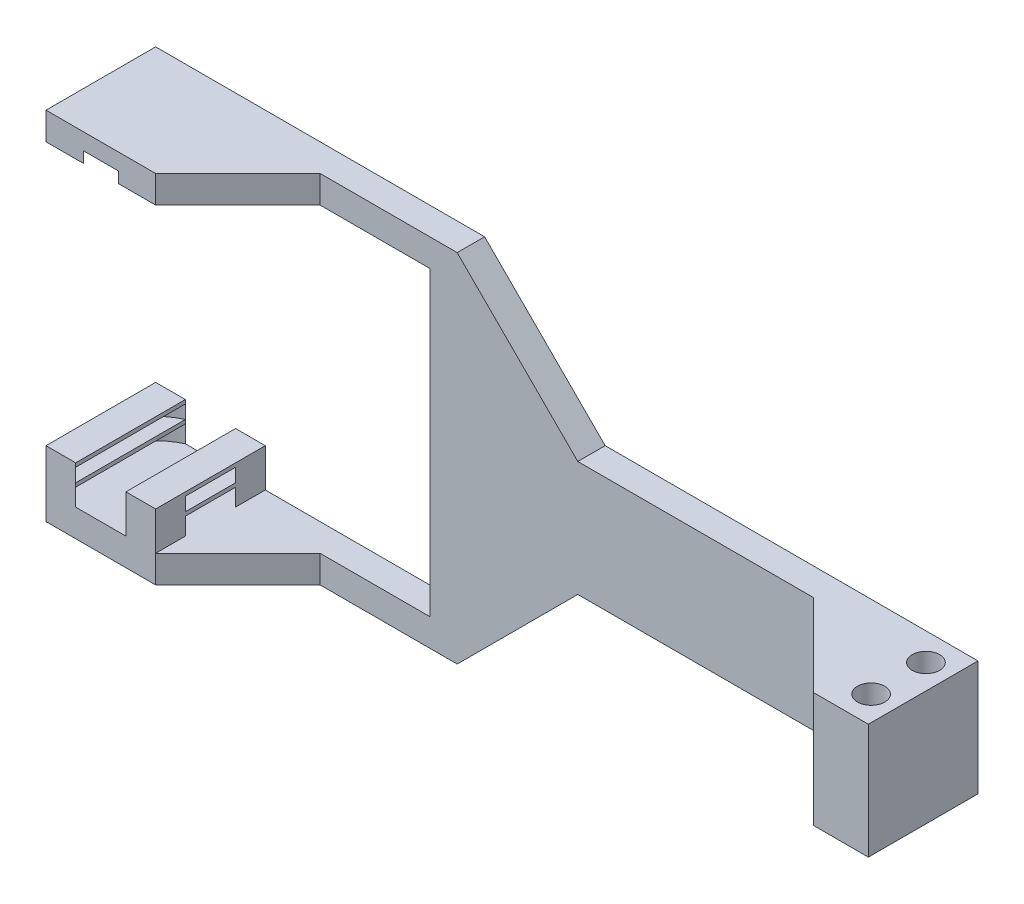
SolidWorks part; units mm, degrees
ref_plane "Face" through (0, 0, 0) normal (0, 0, 1) x (1, 0, 0)
ref_plane "Dessus" through (0, 0, 0) normal (0, 1, 0) x (1, 0, 0)
ref_plane "Droite" through (0, 0, 0) normal (1, 0, 0) x (0, 0, -1)
sketch "Esquisse2" plane through (0, 0, 0) normal (0, 0, 1) x (1, 0, 0)
  line L0 (0, 32.5) -> (0, 27.5)
  line L1 (0, 27.5) -> (55, 27.5)
  line L2 (55, 27.5) -> (55, -27.5)
  line L3 (-109.6717, 0) -> (155.4687, 0) construction
  line L4 (150, -10.5) -> (150, 10.5)
  line L5 (150, 10.5) -> (82, 10.5)
  line L6 (82, 10.5) -> (60, 32.5)
  line L7 (60, 32.5) -> (0, 32.5)
  line L8 (55, 0) -> (-55, 0) construction
  line L9 (60, -32.5) -> (0, -32.5)
  line L10 (82, -10.5) -> (60, -32.5)
  line L11 (150, -10.5) -> (82, -10.5)
  line L12 (0, -27.5) -> (55, -27.5)
  line L13 (0, -32.5) -> (0, -27.5)
  point P16 (150, 0)
  point P17 (55, 0)
  dimension "D1" = 150
  dimension "D2" = 55
  dimension "D3" = 5
  dimension "D4" = 45
  dimension "D5" = 5
  dimension "D6" = 21
  dimension "D7" = 55
extrude "Extrusion1" add sketch "Esquisse2" along normal blind 20
sketch "Esquisse3" plane through (0, -10.5, 0) normal (0, -1, 0) x (1, 0, 0)
  line L0 (93.1782, 10) -> (165.9014, 10) construction
  line L1 (82, 20) -> (150, 20) construction
  line L2 (82, 0) -> (150, 0) construction
  line L3 (150, 20) -> (150, 0) construction
  circle A0 centre (145.5, 15) radius 2.5
  circle A1 centre (145.5, 5) radius 2.5
  dimension "D1" = 5
  dimension "D2" = 4.5
  dimension "D3" = 10
extrude "Enlèv. mat.-Extru.1" cut sketch "Esquisse3" against normal through all
sketch "Esquisse4" plane through (0, -32.5, 0) normal (0, -1, 0) x (1, 0, 0)
  line L0 (20, 20) -> (35, 5)
  line L1 (35, 5) -> (125, 5)
  line L2 (125, 5) -> (140, 20)
  line L3 (140, 20) -> (20, 20)
  line L4 (0, 20) -> (60, 20) construction
  line L5 (0, 0) -> (60, 0) construction
  dimension "D1" = 45
  dimension "D2" = 45
  dimension "D3" = 5
  dimension "D4" = 20
  dimension "D5" = 10
extrude "Enlèv. mat.-Extru.2" cut sketch "Esquisse4" against normal through all
sketch "Esquisse5" plane through (0, 27.5, 0) normal (0, -1, 0) x (1, 0, 0)
  line L0 (-24.3745, 44.3745) -> (41.4579, -21.4579) construction
  line L1 (-13.6771, -13.6771) -> (45.1172, 45.1172) construction
  line L3 (20, 48.0412) -> (20, -30.1038) construction
  line L4 (0, 20) -> (0, 0) construction
  line L6 (0, 0) -> (60, 0) construction
  circle A0 centre (10, 10) radius 10.5
  point P15 (20, 0)
  point P16 (10, 10)
  dimension "D1" = 21
extrude "Enlèv. mat.-Extru.3" cut sketch "Esquisse5" against normal blind 2
sketch "Esquisse6" plane through (0, -27.5, 0) normal (0, 1, 0) x (1, 0, 0)
  line L0 (20, 24.5082) -> (20, -42.6901) construction
  line L1 (-14.1378, -34.1378) -> (61.2755, 41.2755) construction
  line L2 (-13.7534, 13.7534) -> (41.4656, -41.4656) construction
  line L3 (0, -20) -> (0, 0) construction
  line L4 (60, 0) -> (0, 0) construction
  line L5 (14.5826, 0) -> (20, 0)
  line L6 (0, 0) -> (5.4174, 0)
  line L7 (0, 0) -> (0, -5.4174)
  line L8 (0, -20) -> (5.4174, -20)
  line L9 (20, 0) -> (20, -5.4174)
  line L10 (20, -14.5826) -> (20, -20)
  line L11 (14.5826, -20) -> (20, -20)
  line L12 (0, -14.5826) -> (0, -20)
  arc A0 (5.4174, 0) -> (0, -5.4174) centre (10, -10) ccw
  arc A1 (20, -5.4174) -> (14.5826, 0) centre (10, -10) ccw
  arc A2 (14.5826, -20) -> (20, -14.5826) centre (10, -10) ccw
  arc A3 (0, -14.5826) -> (5.4174, -20) centre (10, -10) ccw
  point P6 (20, 0)
  point P7 (10, -10)
  dimension "D1" = 22
extrude "Extrusion2" add sketch "Esquisse6" along normal blind 7
sketch "Esquisse7" plane through (0, 0, 0) normal (-1, 0, 0) x (0, 0, 1)
  line L0 (0, -20.5) -> (0, -32.5) construction
  line L1 (0, -20.5) -> (20, -20.5)
  line L2 (0, -20.5) -> (0, -21.2)
  line L3 (0, -21.2) -> (20, -21.2)
  line L4 (20, -20.5) -> (20, -21.2)
  line L5 (0, -23.65) -> (20, -23.65)
  line L6 (0, -23.65) -> (0, -24.35)
  line L7 (0, -24.35) -> (20, -24.35)
  line L8 (20, -23.65) -> (20, -24.35)
  line L9 (20, -20.5) -> (20, -32.5) construction
  line L10 (14.5826, -20.5) -> (20, -20.5) construction
  line L11 (43.2322, -24) -> (-11.3747, -24) construction
  line L12 (14.5826, -27.5) -> (5.4174, -27.5) construction
  dimension "D1" = 0.7
extrude "Extrusion3" add sketch "Esquisse7" against normal up to surface (20 mm away) up to face at (20, -24, 17.2913)
sketch "Esquisse8" plane through (0, 0, 20) normal (0, 0, 1) x (1, 0, 0)
  line L0 (0, -20.5) -> (20, -20.5) construction
  line L1 (5.4174, -20.5) -> (14.5826, -20.5)
  line L2 (5.4174, -20.5) -> (5.4174, -27.5)
  line L3 (5.4174, -27.5) -> (14.5826, -27.5)
  line L4 (14.5826, -20.5) -> (14.5826, -27.5)
  line L5 (5.4174, -24.35) -> (5.4174, -27.5) construction
extrude "Enlèv. mat.-Extru.4" cut sketch "Esquisse8" against normal through all
